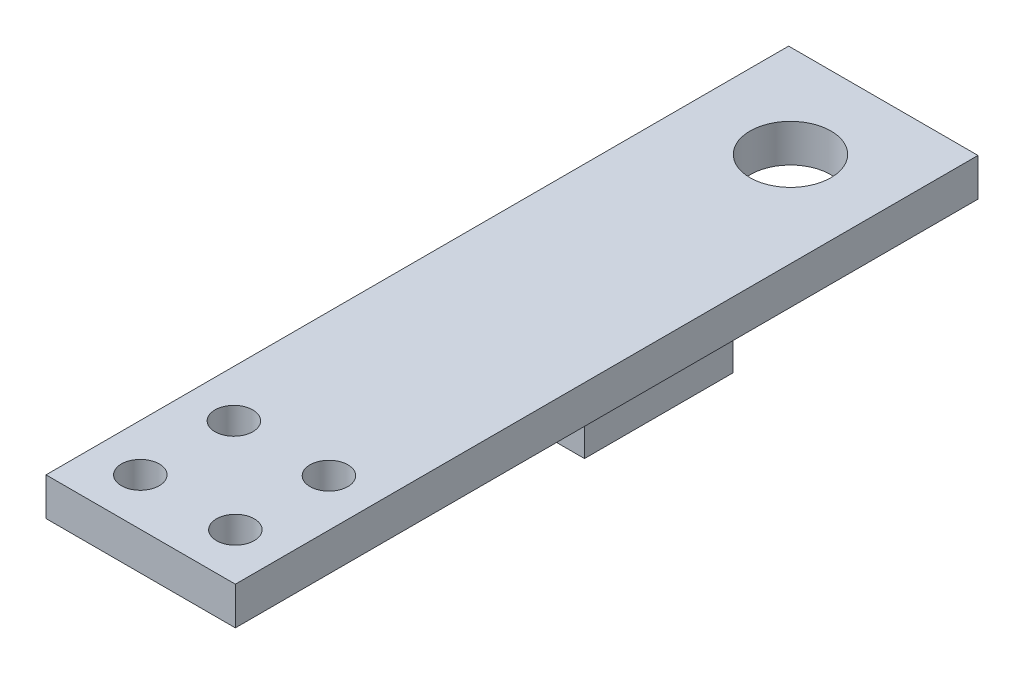
SolidWorks part; units mm, degrees
other "Markup1"
sketch "Sketch4" plane through (-2.55, 1.02, -10) normal (-0.0707, 0.9938, -0.086) x (0.9951, 0.0642, -0.0752)
ref_plane "Front Plane" through (0, 0, 0) normal (0, 0, 1) x (1, 0, 0)
ref_plane "Top Plane" through (0, 0, 0) normal (0, 1, 0) x (1, 0, 0)
ref_plane "Right Plane" through (0, 0, 0) normal (1, 0, 0) x (0, 0, -1)
sketch "Sketch1" plane through (0, 0, 0) normal (0, 1, 0) x (1, 0, 0)
  line L0 (0, -10) -> (0, 10) construction
  line L1 (2.55, -10) -> (-2.55, -10)
  line L2 (2.55, -10) -> (2.55, 10)
  line L3 (2.55, 10) -> (-2.55, 10)
  line L4 (-2.55, -10) -> (-2.55, 10)
  line L5 (2.55, -10) -> (-2.55, 10) construction
  line L6 (2.55, 10) -> (-2.55, -10) construction
  line L7 (-1.8025, 2.15) -> (1.8025, 2.15) construction
  line L8 (-1.8025, 4.15) -> (1.8025, 4.15)
  line L9 (-1.8025, 4.15) -> (-1.8025, 0.15)
  line L10 (-1.8025, 0.15) -> (1.8025, 0.15)
  line L11 (1.8025, 4.15) -> (1.8025, 0.15)
  circle A0 centre (0, 7.5) radius 1.09
  circle A1 centre (-1.28, -6.21) radius 0.51
  circle A2 centre (-1.28, -8.73) radius 0.51
  circle A5 centre (1.28, -6.21) radius 0.51
  circle A6 centre (1.28, -8.73) radius 0.51
  point P0 (0, 0)
  point P9 (0, 0)
  point P11 (0, 4.15)
  dimension "D3" = 2.18
  dimension "D8" = 1.02
  dimension "D1" = 5.1
  dimension "D2" = 20
  dimension "D4" = 2.5
  dimension "D5" = 12.15
  dimension "D6" = 4
  dimension "D7" = 3.605
  dimension "D9" = 1.27
  dimension "D10" = 1.27
  dimension "D11" = 2.52
extrude "Body" add sketch "Sketch1" along normal blind 1.02 contours L9 L8 L11 L10 | L2 L1 L4 L3 | A0 | A1 | A2 | A6 | A5
sketch "Sketch3" plane through (0, 1.02, 0) normal (0, 1, 0) x (1, 0, 0)
  line L0 (-1.8025, 0.15) -> (1.8025, 0.15) construction
  line L1 (-1.8025, 4.15) -> (-1.8025, 0.15) construction
  line L2 (-1.8025, 4.15) -> (1.8025, 4.15) construction
  line L3 (1.8025, 4.15) -> (1.8025, 0.15) construction
  line L4 (-1.8025, 0.15) -> (1.8025, 0.15)
  line L5 (-1.8025, 4.15) -> (-1.8025, 0.15)
  line L6 (-1.8025, 4.15) -> (1.8025, 4.15)
  line L7 (1.8025, 4.15) -> (1.8025, 0.15)
extrude "Sensor" add sketch "Sketch3" against normal blind 2.52
